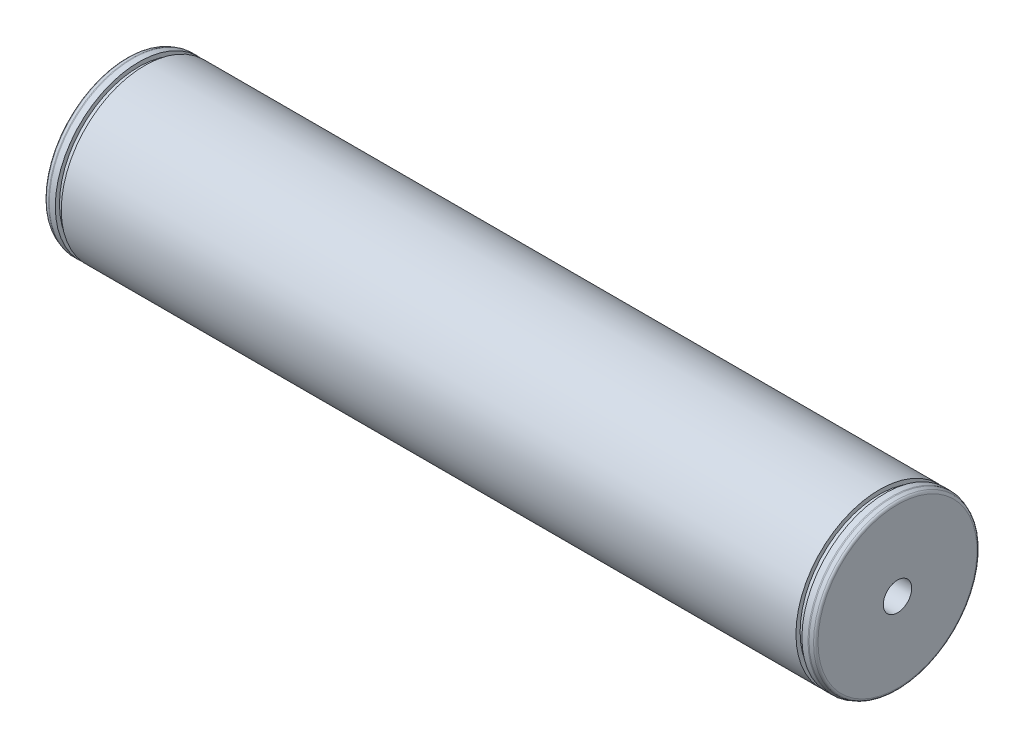
SolidWorks part; units mm, degrees
revolve "Base-Revolve" add sketch "Sketch1" angle 360 about L0
sketch "Sketch1" plane through (0, 0, 0) normal (0, 0, 1) x (1, 0, 0)
  line L0 (-138.5, 0) -> (138.5, 0) construction
  line L1 (132, 30) -> (0, 30)
  line L2 (132, 30) -> (132, 28.5)
  line L4 (-138.5, 0) -> (115.5555, 0)
  line L5 (137.842, 29.5115) -> (136.6657, 29.9397)
  line L9 (138.5, 5.1) -> (118.5, 5.1)
  line L10 (118.5, 5.1) -> (115.5555, 0)
  line L11 (0, 0) -> (0, 78.5782) construction
  line L13 (0, 30) -> (-132, 30)
  line L14 (-132, 28.5) -> (-134.15, 28.5)
  line L15 (-134.15, 28.5) -> (-134.15, 30)
  line L16 (-134.15, 30) -> (-136.3237, 30)
  line L17 (-138.5, 28.5719) -> (-138.5, 0)
  line L19 (-137.842, 29.5115) -> (-136.6657, 29.9397)
  line L20 (-132, 30) -> (-132, 28.5)
  line L22 (138.5, 28.5719) -> (138.5, 5.1)
  line L23 (134.15, 30) -> (136.3237, 30)
  line L24 (134.15, 28.5) -> (134.15, 30)
  line L25 (132, 28.5) -> (134.15, 28.5)
  arc A0 (138.5, 28.5719) -> (137.842, 29.5115) centre (137.5, 28.5719) ccw
  arc A1 (-136.3237, 30) -> (-136.6657, 29.9397) centre (-136.3237, 29) ccw
  arc A2 (136.3237, 30) -> (136.6657, 29.9397) centre (136.3237, 29) cw
  arc A3 (-138.5, 28.5719) -> (-137.842, 29.5115) centre (-137.5, 28.5719) cw
  point P15 (136.5, 30)
  dimension "D6" = 2
  dimension "D16" = 20
  dimension "D17" = 1
  dimension "D3" = 57
  dimension "D4" = 2.15
  dimension "D5" = 6.5
  dimension "D7" = 264
  dimension "D8" = 277
  dimension "D12" = 60
  dimension "D23" = 10.2
  dimension "D24" = 20
  dimension "D25" = 60
cosmetic thread "Cosmetic Thread2"
ref_plane "Front" through (0, 0, 0) normal (0, 0, 1) x (1, 0, 0)
ref_plane "Top" through (0, 0, 0) normal (0, 1, 0) x (1, 0, 0)
ref_plane "Right" through (0, 0, 0) normal (1, 0, 0) x (0, 0, -1)
